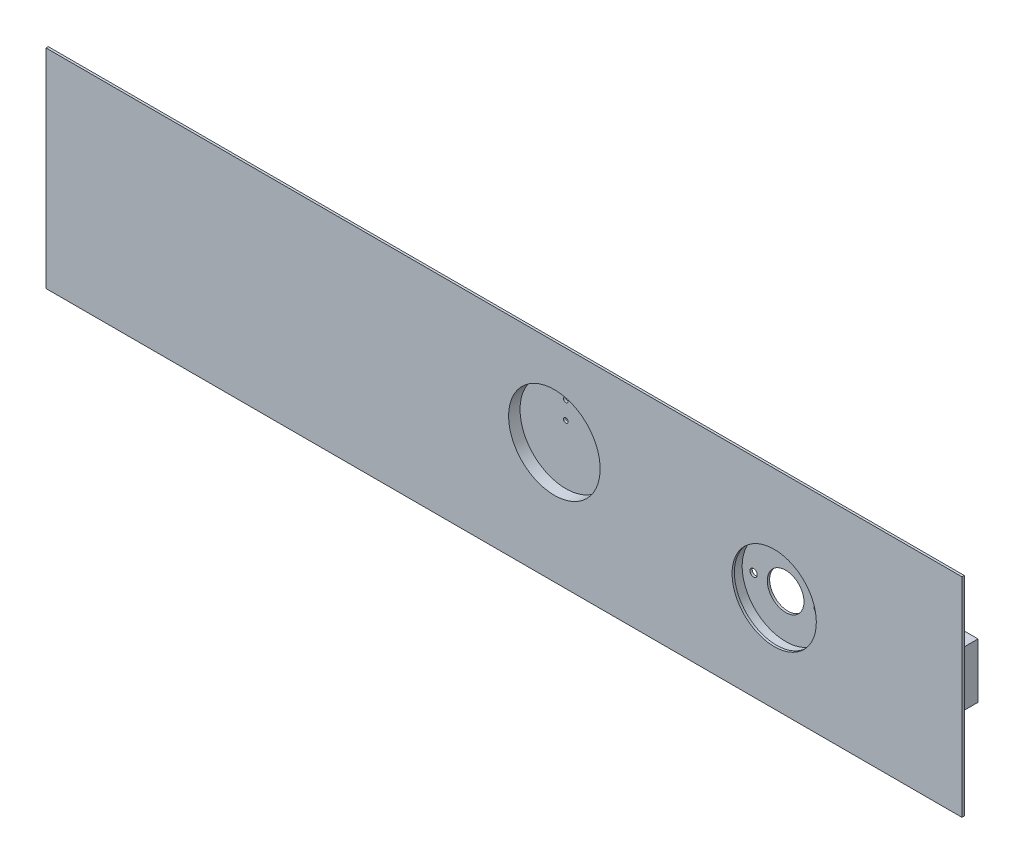
SolidWorks part; units mm, degrees
ref_plane "Front Plane" through (0, 0, 0) normal (0, 0, 1) x (1, 0, 0)
ref_plane "Top Plane" through (0, 0, 0) normal (0, 1, 0) x (1, 0, 0)
ref_plane "Right Plane" through (0, 0, 0) normal (1, 0, 0) x (0, 0, -1)
sketch "Sketch1" plane through (0, 0, 0) normal (0, 0, 1) x (1, 0, 0)
  line L0 (22.225, 0) -> (-22.225, 0) construction
  circle A0 centre (0, 0) radius 12.7
  circle A1 centre (-22.225, 0) radius 2.54
  circle A2 centre (22.225, 0) radius 2.54
  circle A3 centre (0, 0) radius 31.75
  point P6 (0, 0)
  dimension "D1" = 25.4
  dimension "D3" = 5.08
  dimension "D4" = 63.5
  dimension "D2" = 44.45
extrude "Boss-Extrude1" add sketch "Sketch1" along normal blind 1.5875
sketch "Sketch2" plane through (0, 0, 1.5875) normal (0, 0, 1) x (1, 0, 0)
  circle A0 centre (0, 0) radius 38.1
  dimension "D1" = 76.2
ref_plane "Front panel" through (0, 0, 7.9375) normal (0, 0, 1) x (1, 0, 0)
sketch "Sketch3" plane through (0, 0, 7.9375) normal (0, 0, 1) x (1, 0, 0)
  line L1 (-504.825, 77.7875) -> (130.175, 77.7875)
  line L2 (-504.825, 77.7875) -> (-504.825, -66.675)
  line L3 (-504.825, -66.675) -> (130.175, -66.675)
  line L4 (130.175, 77.7875) -> (130.175, -66.675)
  circle A2 centre (0, 0) radius 29.21
  circle A3 centre (0, 0) radius 12.7 construction
  dimension "D5" = 58.42
  dimension "D1" = 144.4625
  dimension "D2" = 635
  dimension "D3" = 130.175
  dimension "D4" = 66.675
extrude "Boss-Extrude2" add sketch "Sketch3" along normal blind 1.5875 separate body
sketch "Sketch4" plane through (0, 0, 7.9375) normal (0, 0, -1) x (-1, 0, 0)
  circle A0 centre (0, 0) radius 41.275
  circle A1 centre (0, 0) radius 31.75 construction
  dimension "D1" = 82.55
sketch "Sketch5" plane through (0, 0, 1.5875) normal (0, 0, -1) x (-1, 0, 0)
  circle A0 centre (0, 0) radius 31.75 construction
  circle A1 centre (0, 0) radius 31.75
loft "Loft1" add profiles "Sketch4", "Sketch5"
ref_plane "spare mount surface" through (0, 0, 0) normal (0, 0, -1) x (-1, 0, 0)
sketch "Sketch6" plane through (0, 0, 7.9375) normal (0, 0, -1) x (-1, 0, 0)
  circle A1 centre (0, 0) radius 30.1625
  circle A2 centre (0, 0) radius 31.75 construction
  dimension "D1" = 1.5875
extrude "Timer hole" cut sketch "Sketch6" along normal up to surface (6.35 mm away) up to face at (24.765, 0, 1.5875)
sketch "Sketch7" plane through (0, 0, 7.9375) normal (0, 0, -1) x (-1, 0, 0)
  line L1 (-95.25, 19.05) -> (-114.3, 19.05)
  line L2 (-95.25, 19.05) -> (-95.25, -19.05)
  line L3 (-95.25, -19.05) -> (-114.3, -19.05)
  line L4 (-114.3, 19.05) -> (-114.3, -19.05)
  point P4 (-95.25, 0)
  dimension "D1" = 95.25
  dimension "D2" = 38.1
  dimension "D3" = 19.05
extrude "Soak light" add sketch "Sketch7" along normal blind 25.4
sketch "Sketch8" plane through (0, 0, 7.9375) normal (0, 0, -1) x (-1, 0, 0)
  line L0 (504.825, -66.675) -> (-130.175, -66.675) construction
  line L1 (0, 0) -> (152.4, 0) construction
  circle A0 centre (152.4, 17.145) radius 44.45
  circle A1 centre (0, 0) radius 38.1 construction
  circle A2 centre (0, 0) radius 38.1 construction
  point P10 (0, 0)
  dimension "D3" = 88.9
  dimension "D1" = 152.4
  dimension "D2" = 83.82
sketch "Sketch9" plane through (0, 0, 0) normal (0, 0, -1) x (-1, 0, 0)
  circle A0 centre (152.4, 17.145) radius 31.75
  circle A1 centre (152.4, 17.145) radius 44.45 construction
  circle A2 centre (0, 0) radius 31.75 construction
loft "spare mount" add profiles "Sketch8", "Sketch9"
sketch "Sketch10" plane through (0, 0, 7.9375) normal (0, 0, -1) x (-1, 0, 0)
  circle A0 centre (152.4, 17.145) radius 31.75 construction
  circle A1 centre (152.4, 17.145) radius 31.75
extrude "Cut-Extrude1" cut sketch "Sketch10" along normal offset from surface 1.5875 and the other way through all up to face at (-184.15, 17.145, 0)
sketch "Sketch11" plane through (0, 0, 0) normal (0, 0, -1) x (-1, 0, 0)
  line L0 (152.4, 77.7875) -> (152.4, -66.675) construction
  line L1 (-130.175, 77.7875) -> (504.825, 77.7875) construction
  line L2 (504.825, -66.675) -> (-130.175, -66.675) construction
  line L3 (160.6325, 40.386) -> (144.1675, 40.386) construction
  line L4 (144.1675, 28.067) -> (160.6325, 28.067) construction
  line L5 (144.1675, 24.765) -> (160.6325, 24.765) construction
  line L6 (144.1675, 37.084) -> (160.6325, 37.084) construction
  line L7 (504.825, -66.675) -> (-130.175, -66.675) construction
  circle A0 centre (152.4, 26.416) radius 1.651
  circle A1 centre (152.4, 38.735) radius 1.651
  circle A3 centre (152.4, 17.145) radius 31.75 construction
  circle A5 centre (152.4, 17.145) radius 31.75 construction
  point P20 (152.4, 40.386)
  point P21 (152.4, 28.067)
  point P22 (152.4, 24.765)
  point P25 (152.4, 37.084)
  dimension "D1" = 9.017
  dimension "D2" = 91.44
  dimension "D3" = 15.621
extrude "Cut-Extrude2" cut sketch "Sketch11" against normal through all
